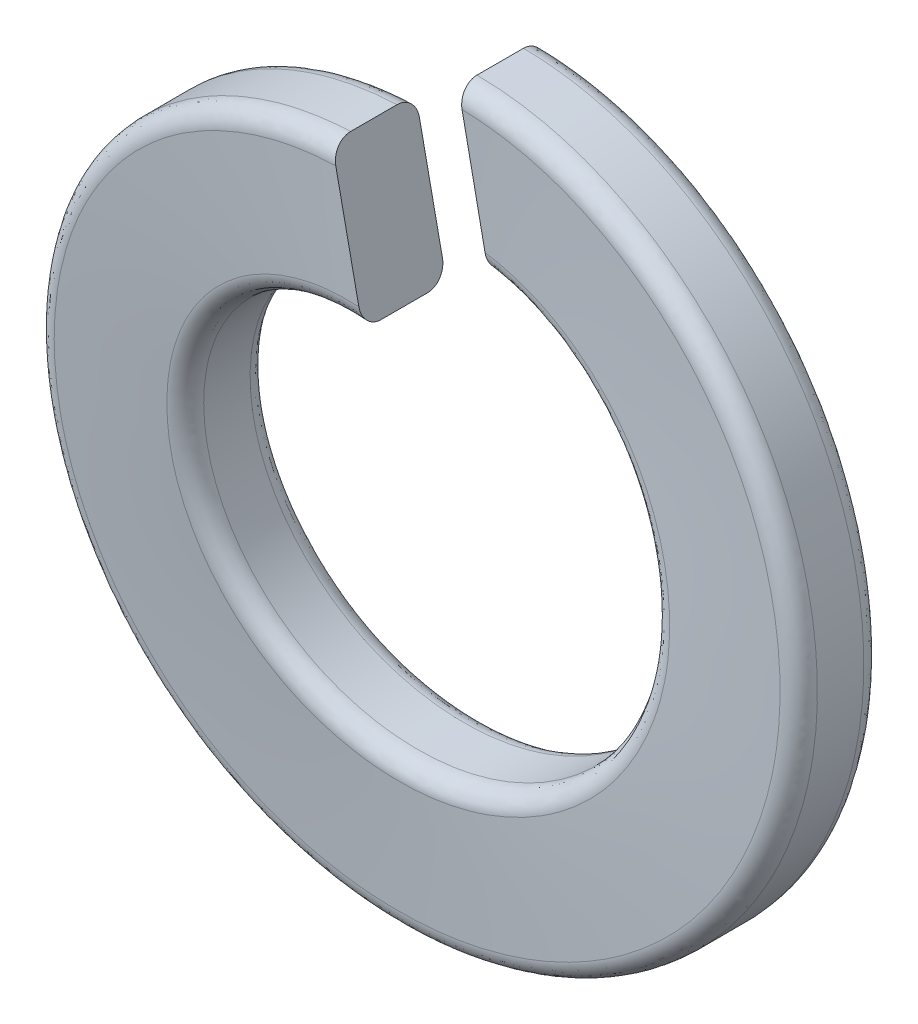
SolidWorks part; units mm, degrees
material "Plain Carbon Steel"
ref_plane "Front Plane" through (0, 0, 0) normal (0, 0, 1) x (1, 0, 0)
ref_plane "Top Plane" through (0, 0, 0) normal (0, 1, 0) x (1, 0, 0)
ref_plane "Right Plane" through (0, 0, 0) normal (1, 0, 0) x (0, 0, -1)
sketch "Sketch1" plane through (0, 0, 0) normal (0, 0, 1) x (1, 0, 0)
  line L0 (0, -3.8) -> (0, 3.8) construction
  line L1 (-0.1658, 3.7964) -> (0.1691, 2.1935) construction
  line L2 (0, 0) -> (-1.1, -1.9053) construction
  line L3 (0, 2.2) -> (-0.3312, 3.7855) construction
  line L4 (0, 0) -> (-0.3312, 3.7855) construction
  line L5 (-0.1658, 3.7964) -> (0, 0) construction
  circle A0 centre (0, 0) radius 3.8 construction
  circle A1 centre (0, 0) radius 2.2 construction
  point P6 (0, -2.2)
  dimension "ID" = 4.4
  dimension "OD" = 7.6
  dimension "D2" = 5
  dimension "D1" = 30
  dimension "D3" = 2.5
sketch "Sketch2" plane through (0, 0, 0) normal (1, 0, 0) x (0, 0, -1)
  line L0 (-1.05, 0) -> (1.05, 0) construction
  line L1 (0, -3.8) -> (0, 3.8) construction
  line L2 (-1.05, 3.8) -> (-0.15, 3.8) construction
  line L3 (-1.05, 3.8) -> (-1.05, 2.2) construction
  line L4 (-1.05, 2.2) -> (-0.15, 2.2) construction
  line L5 (-0.15, 3.8) -> (-0.15, 2.2) construction
  line L6 (0, -3.8) -> (0, 3.8) construction
  line L12 (-0.45, -2.2) -> (0.45, -2.2) construction
  line L13 (-0.45, -2.2) -> (-0.45, -3.8) construction
  line L14 (-0.45, -3.8) -> (0.45, -3.8) construction
  line L15 (0.45, -2.2) -> (0.45, -3.8) construction
  point P8 (-0.6, 3.8)
  point P13 (0.45, -3.6)
  point P15 (1.05, 3.8)
  point P19 (0.6, 3.8)
  dimension "Thickness" = 0.9
  dimension "Helix Height" = 1.2
  dimension "Height" = 2.1
  dimension "Radius" = 0.2
ref_plane "Plane1" through (0, 0, 0.6) normal (0, 0, 1) x (1, 0, 0)
sketch "Sketch3" plane through (0, 0, 0.6) normal (0, 0, 1) x (1, 0, 0)
  circle A0 centre (0, 0) radius 3.8 construction
  circle A1 centre (0, 0) radius 3.8
curve "Helix/Spiral1" pitch 1.2012 height 1.2 turns 0.999
ref_plane "Plane2" through (0.4403, 0.092, 0) normal (0.9789, 0.2045, 0) x (0.0072, -0.0342, -0.9994)
sketch "Sketch4" plane through (0.4699, -0.0497, 0.0051) normal (0.9789, 0.2045, 0) x (0.0072, -0.0342, -0.9994)
  line L0 (-1.1794, 3.8255) -> (-0.28, 3.857) construction
  line L10 (-1.1247, 2.2603) -> (-0.2252, 2.2918) construction
  line L12 (-1.1813, 3.8791) -> (-0.2819, 3.9105)
  line L13 (-0.2819, 3.9105) -> (-0.2252, 2.2918)
  line L14 (-1.1247, 2.2603) -> (-0.2252, 2.2918)
  line L15 (-1.1813, 3.8791) -> (-1.1247, 2.2603)
sweep "Sweep1" add profiles "Sketch4" path "Helix/Spiral1"
sketch "Sketch5" plane through (0, 0, 0) normal (0, 0, 1) x (1, 0, 0)
  line L0 (0, 2.2) -> (-0.3312, 3.7855) construction
  line L1 (-0.1658, 3.7964) -> (0.1691, 2.1935) construction
  line L2 (0, 2.2) -> (-0.3312, 3.7855)
  line L3 (-0.1658, 3.7964) -> (0.1691, 2.1935)
  circle A0 centre (0, 0) radius 2.2 construction
  circle A1 centre (0, 0) radius 3.8 construction
  arc A2 (0.1691, 2.1935) -> (0, 2.2) centre (0, 0) ccw
  arc A3 (-0.1658, 3.7964) -> (-0.3312, 3.7855) centre (0, 0) ccw
extrude "Cut-Extrude1" cut sketch "Sketch5" against normal through all
fillet "Fillet1" radius 0.2 4 edges
equation "\"D3@Helix/Spiral1\"=\"Helix Height@Sketch2\""
equation "\"D7@Helix/Spiral1\"=90+\"D2@Sketch1\""
equation "\"D1@Fillet1\"=\"Radius@Sketch2\""
equation "\"D3@Sketch1\"=\"D2@Sketch1\"/2"
